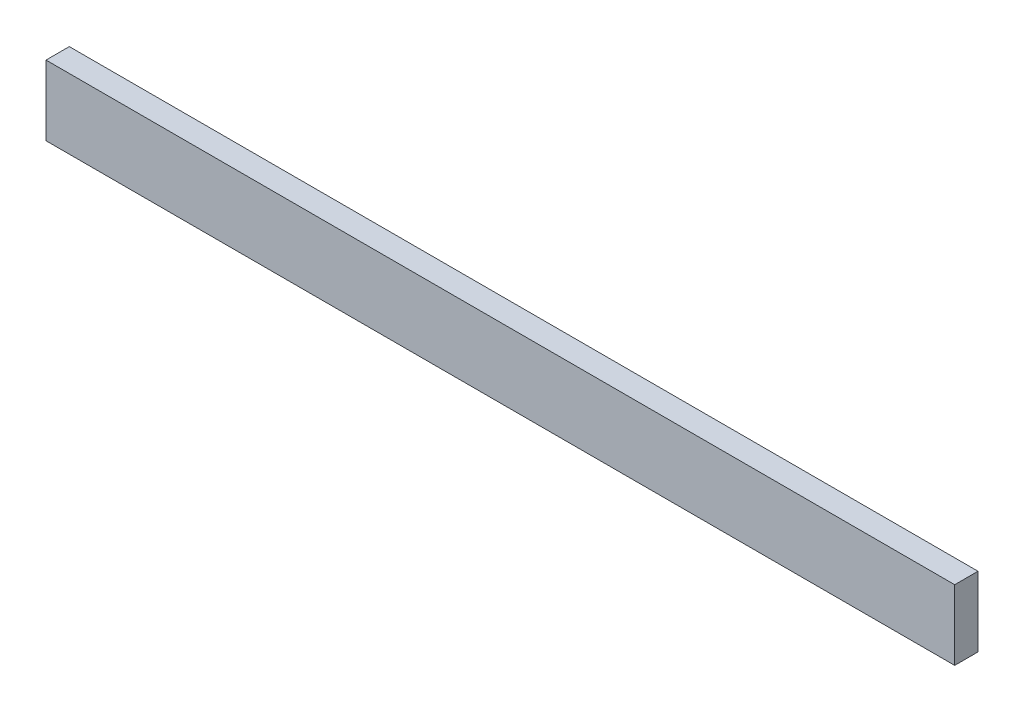
SolidWorks part; units mm, degrees
ref_plane "Front Plane" through (0, 0, 0) normal (0, 0, 1) x (1, 0, 0)
ref_plane "Top Plane" through (0, 0, 0) normal (0, 1, 0) x (1, 0, 0)
ref_plane "Right Plane" through (0, 0, 0) normal (1, 0, 0) x (0, 0, -1)
sketch "Sketch2" plane through (0, 0, 0) normal (0, 0, 1) x (1, 0, 0)
  line L1 (0, 0) -> (247.65, 0)
  line L2 (0, 0) -> (0, 19.05)
  line L3 (0, 19.05) -> (247.65, 19.05)
  line L4 (247.65, 0) -> (247.65, 19.05)
  dimension "D1" = 247.65
  dimension "D2" = 19.05
extrude "Boss-Extrude1" add sketch "Sketch2" along normal blind 6.35
